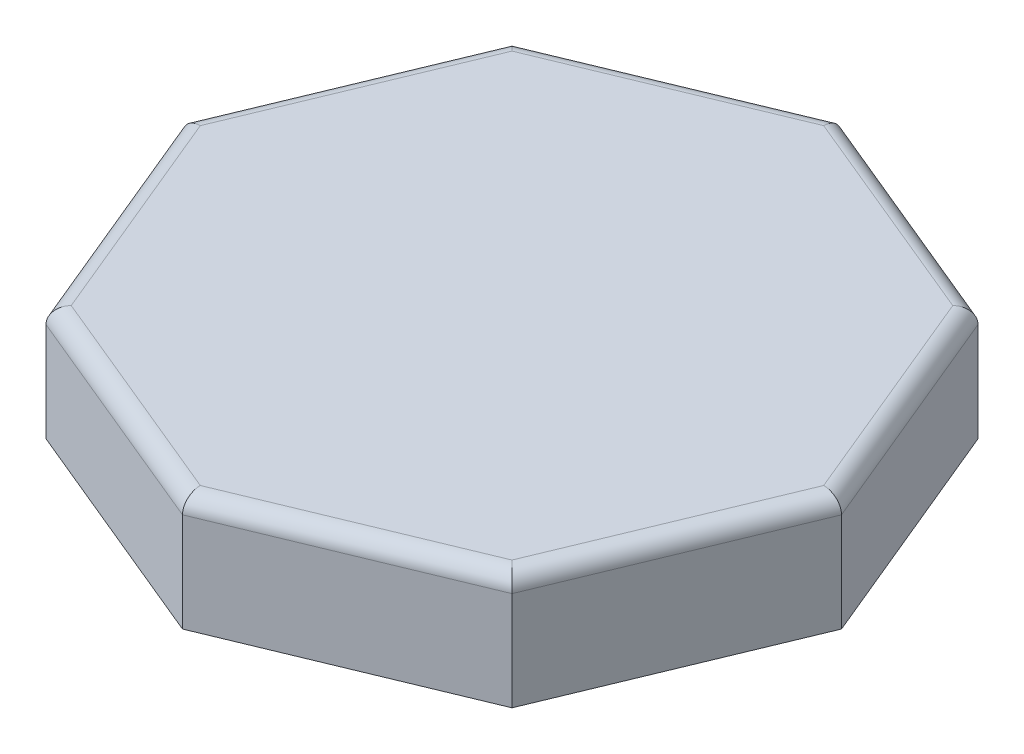
SolidWorks part; units mm, degrees
ref_plane "Front Plane" through (0, 0, 0) normal (0, 0, 1) x (1, 0, 0)
ref_plane "Top Plane" through (0, 0, 0) normal (0, 1, 0) x (1, 0, 0)
ref_plane "Right Plane" through (0, 0, 0) normal (1, 0, 0) x (0, 0, -1)
sketch "Sketch3" plane through (0, 0, 0) normal (0, 1, 0) x (1, 0, 0)
  line L0 (0, 0) -> (0, -199.9041) construction
  line L3 (0, 0) -> (0, 199.9041) construction
  line L4 (0, 0) -> (199.9041, 0) construction
  line L5 (0, 0) -> (-199.9041, 0) construction
  line L6 (0, 0) -> (141.3536, -141.3536) construction
  line L7 (0, 0) -> (141.3536, 141.3536) construction
  line L8 (0, 0) -> (-141.3536, 141.3536) construction
  line L9 (0, 0) -> (-141.3536, -141.3536) construction
  line L10 (0, 199.9041) -> (-141.3536, 141.3536)
  line L11 (-141.3536, 141.3536) -> (-199.9041, 0)
  line L12 (-199.9041, 0) -> (-141.3536, -141.3536)
  line L13 (-141.3536, -141.3536) -> (0, -199.9041)
  line L14 (0, -199.9041) -> (141.3536, -141.3536)
  line L15 (141.3536, -141.3536) -> (199.9041, 0)
  line L16 (199.9041, 0) -> (141.3536, 141.3536)
  line L17 (141.3536, 141.3536) -> (0, 199.9041)
  circle A0 centre (0, 0) radius 199.9041 construction
  dimension "D1" = 153
extrude "Boss-Extrude1" add sketch "Sketch3" along normal blind 70
shell "Shell1" thickness 3
ref_plane "Plane1" through (0, 90, 0) normal (0, 1, 0) x (1, 0, 0)
sketch "Sketch4" plane through (0, 90, 0) normal (0, 1, 0) x (1, 0, 0)
  point P0 (0, 0)
ref_plane "Plane2" through (331, 0, 0) normal (1, 0, 0) x (0, 0, -1)
sketch "Sketch5" plane through (331, 0, 0) normal (1, 0, 0) x (0, 0, -1)
  line L0 (-141.3536, 0) -> (0, 0) construction
  line L1 (-50, 0) -> (50, 0)
  line L2 (-50, 0) -> (-50, 80)
  line L3 (-50, 80) -> (50, 80)
  line L4 (50, 0) -> (50, 80)
  dimension "D1" = 100
  dimension "D2" = 50
  dimension "D3" = 80
extrude "Cut-Extrude2" cut sketch "Sketch5" against normal blind 30
fillet "Fillet1" radius 10 8 edges at (170.6289, 70, 70.6768) (70.6768, 70, 170.6289) (-70.6768, 70, 170.6289) (-170.6289, 70, 70.6768) (-170.6289, 70, -70.6768) (-70.6768, 70, -170.6289) (70.6768, 70, -170.6289) (170.6289, 70, -70.6768)
fillet "Fillet2" radius 3 8 edges at (167.8572, 67, -69.5287) (167.8572, 67, 69.5287) (69.5287, 67, 167.8572) (-69.5287, 67, 167.8572) (-167.8572, 67, 69.5287) (-167.8572, 67, -69.5287) (-69.5287, 67, -167.8572) (69.5287, 67, -167.8572)
